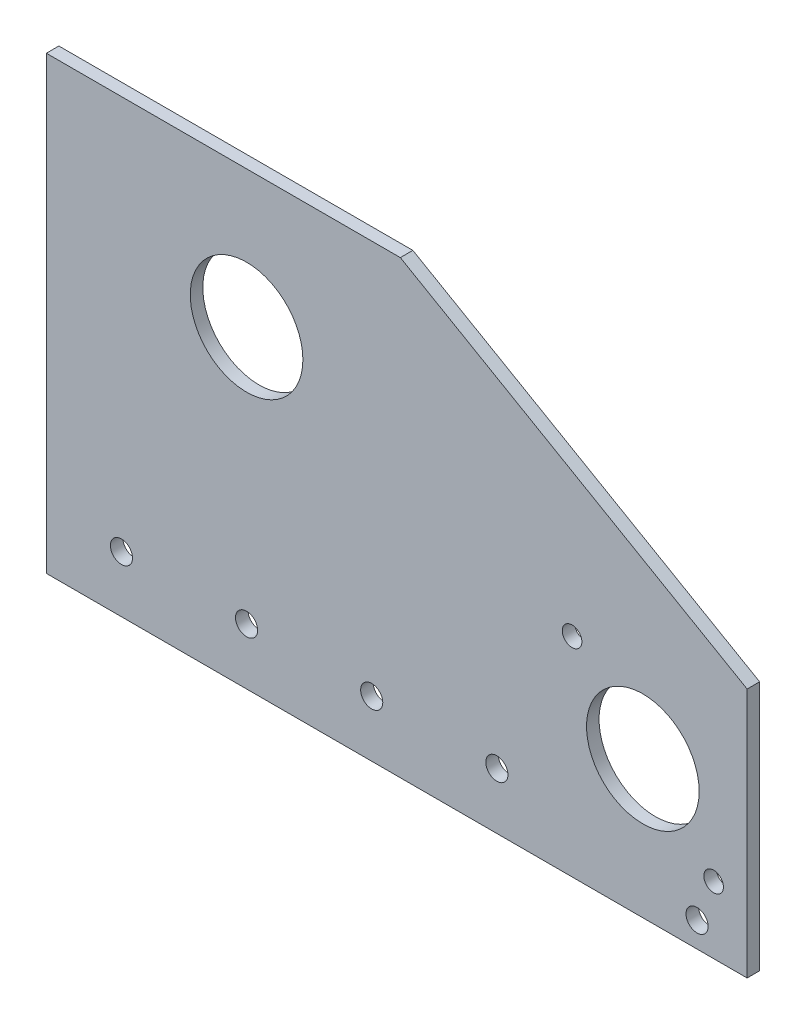
SolidWorks part; units mm, degrees
material "6061-T6 (SS)"
ref_plane "Front Plane" through (0, 0, 0) normal (0, 0, 1) x (1, 0, 0)
ref_plane "Top Plane" through (0, 0, 0) normal (0, 1, 0) x (1, 0, 0)
ref_plane "Right Plane" through (0, 0, 0) normal (1, 0, 0) x (0, 0, -1)
sketch "Sketch1" plane through (0, 0, 0) normal (0, 0, 1) x (1, 0, 0)
  line L1 (-88.9, 57.15) -> (88.9, 57.15)
  line L2 (-88.9, 57.15) -> (-88.9, -57.15)
  line L3 (-88.9, -57.15) -> (88.9, -57.15)
  line L4 (88.9, 57.15) -> (88.9, -57.15)
  line L5 (-88.9, 57.15) -> (88.9, -57.15) construction
  line L6 (-88.9, -57.15) -> (88.9, 57.15) construction
  point P0 (0, 0)
  dimension "D1" = 114.3
  dimension "D2" = 177.8
extrude "Boss-Extrude1" add sketch "Sketch1" along normal blind 3.175
sketch "Sketch2" plane through (0, 0, 3.175) normal (0, 0, 1) x (1, 0, 0)
  line L0 (-88.9, -57.15) -> (88.9, -57.15) construction
  line L1 (-88.9, 57.15) -> (-88.9, -57.15) construction
  circle A0 centre (-38.1, 22.352) radius 14.2875
  dimension "D1" = 28.575
  dimension "D2" = 79.502
  dimension "D3" = 50.8
extrude "Cut-Extrude1" cut sketch "Sketch2" against normal blind 3.175 contours A0
hole_wizard "#10 Clearance Hole1" positions "Sketch4" profile "Sketch3" hole size "#10" standard "ANSI Inch" end condition through all
sketch "Sketch4" plane through (0, 0, 3.175) normal (0, 0, 1) x (1, 0, 0)
  line L0 (-88.9, -57.15) -> (88.9, -57.15) construction
  line L1 (-88.9, 57.15) -> (-88.9, -57.15) construction
  point P0 (-69.85, -42.8625)
  point P2 (-38.1, -42.8625)
  point P4 (-6.35, -42.8625)
  point P17 (25.4, -42.8625)
  dimension "D1" = 14.2875
  dimension "D2" = 19.05
  dimension "D3" = 31.75
  dimension "D4" = 50.8
  dimension "D5" = 31.75
sketch "Sketch3" plane through (-69.85, -42.8625, 3.175) normal (1, 0, 0) x (0, -1, 0)
  line L0 (0, 0) -> (0, 3.175)
  line L1 (0, 3.175) -> (2.8067, 3.175)
  line L2 (2.8067, 3.175) -> (2.8067, 0)
  line L5 (2.8067, 0) -> (0, 0)
  line L11 (0, -6.35) -> (0, 107.95) construction
  dimension "Thru Hole Dia." = 5.6134
  dimension "Thru Hole Depth" = 3.175
sketch "Sketch5" plane through (0, 0, 3.175) normal (0, 0, 1) x (1, 0, 0)
  line L1 (44.4827, -4.2645) -> (80.4037, -4.2645) construction
  line L2 (44.4827, -4.2645) -> (44.4827, -40.1855) construction
  line L3 (44.4827, -40.1855) -> (80.4037, -40.1855) construction
  line L4 (80.4037, -4.2645) -> (80.4037, -40.1855) construction
  line L5 (44.4827, -4.2645) -> (80.4037, -40.1855) construction
  line L6 (44.4827, -40.1855) -> (80.4037, -4.2645) construction
  line L7 (62.4432, -22.225) -> (62.4432, -57.15) construction
  line L8 (-88.9, -57.15) -> (88.9, -57.15) construction
  circle A0 centre (-38.1, 22.352) radius 109.982 construction
  circle A1 centre (62.4432, -22.225) radius 14.2875
  circle A2 centre (44.4827, -4.2645) radius 2.4892
  circle A3 centre (80.4037, -40.1855) radius 2.4892
  dimension "D1" = 219.964
  dimension "D2" = 28.575
  dimension "D5" = 4.9784
  dimension "D3" = 25.4
  dimension "D4" = 34.925
extrude "Cut-Extrude2" cut sketch "Sketch5" against normal through all
chamfer "Chamfer1" distance 50.8 angle 60 1 edges at (88.9, 57.15, 1.5875)
hole_wizard "#10 Clearance Hole2" positions "Sketch8" profile "Sketch7" hole size "#10" standard "ANSI Inch" end condition through all
sketch "Sketch8" plane through (0, 0, 0) normal (0, 0, -1) x (-1, 0, 0)
  line L0 (-88.9, -57.15) -> (-88.9, 6.35) construction
  line L1 (88.9, -57.15) -> (-88.9, -57.15) construction
  point P0 (-76.2, -50.8)
  dimension "D1" = 12.7
  dimension "D2" = 6.35
sketch "Sketch7" plane through (76.2, -50.8, 0) normal (1, 0, 0) x (0, 1, 0)
  line L0 (0, 0) -> (0, 3.175)
  line L1 (0, 3.175) -> (2.8067, 3.175)
  line L2 (2.8067, 3.175) -> (2.8067, 0)
  line L5 (2.8067, 0) -> (0, 0)
  line L11 (0, -6.35) -> (0, 107.95) construction
  dimension "Thru Hole Dia." = 5.6134
  dimension "Thru Hole Depth" = 3.175
